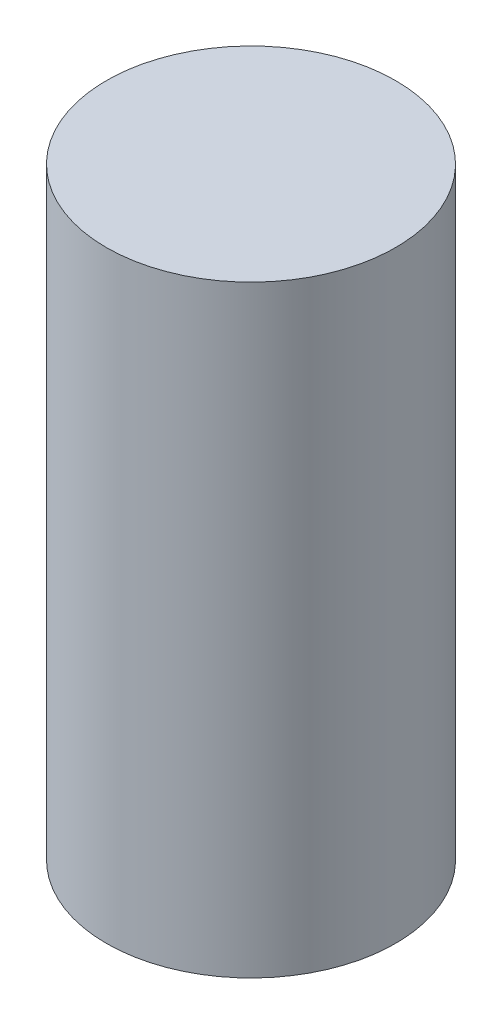
SolidWorks part; units mm, degrees
ref_plane "Front Plane" through (0, 0, 0) normal (0, 0, 1) x (1, 0, 0)
ref_plane "Top Plane" through (0, 0, 0) normal (0, 1, 0) x (1, 0, 0)
ref_plane "Right Plane" through (0, 0, 0) normal (1, 0, 0) x (0, 0, -1)
sketch "Sketch2" plane through (0, 0, 0) normal (0, 1, 0) x (1, 0, 0)
  circle A0 centre (0, 0) radius 0.6
  dimension "D1" = 1.2
extrude "Boss-Extrude1" add sketch "Sketch2" along normal blind 2.5
